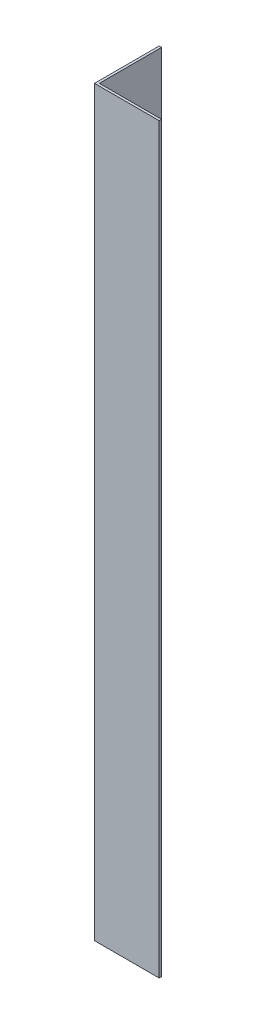
SolidWorks part; units mm, degrees
material "1060 Сплав"
ref_plane "Спереди" through (0, 0, 0) normal (0, 0, 1) x (1, 0, 0)
ref_plane "Сверху" through (0, 0, 0) normal (0, 1, 0) x (1, 0, 0)
ref_plane "Справа" through (0, 0, 0) normal (1, 0, 0) x (0, 0, -1)
sketch "Эскиз1" plane through (0, 0, 0) normal (0, 1, 0) x (1, 0, 0)
  line L0 (0, 0) -> (0, 20)
  line L1 (0, 20) -> (0.75, 20)
  line L2 (0.75, 20) -> (0.75, 0.75)
  line L3 (0.75, 0.75) -> (20, 0.75)
  line L4 (20, 0.75) -> (20, 0)
  line L5 (20, 0) -> (0, 0)
  dimension "D1" = 0.75
  dimension "D2" = 20
extrude "Бобышка-Вытянуть1" add sketch "Эскиз1" along normal blind 229.75
